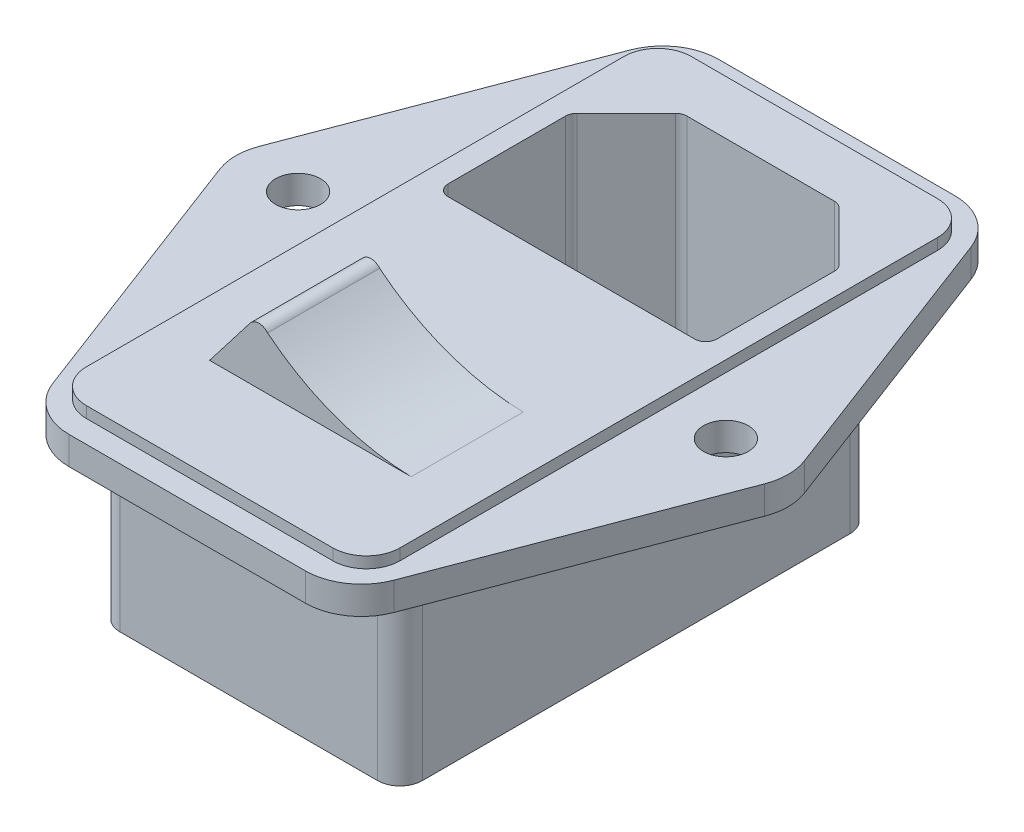
SolidWorks part; units mm, degrees
ref_plane "Front Plane" through (0, 0, 0) normal (0, 0, 1) x (1, 0, 0)
ref_plane "Top Plane" through (0, 0, 0) normal (0, 1, 0) x (1, 0, 0)
ref_plane "Right Plane" through (0, 0, 0) normal (1, 0, 0) x (0, 0, -1)
sketch "Sketch1" plane through (0, 0, 0) normal (0, 1, 0) x (1, 0, 0)
  line L0 (0, 44.6457) -> (0, -41.2867) construction
  line L1 (-19.1, 0) -> (19.1, 0) construction
  line L2 (25, 0) -> (14, -29)
  line L3 (0, 29) -> (14, 29)
  line L4 (14, 29) -> (25, 0)
  line L5 (0, -29) -> (14, -29)
  line L6 (0, 29) -> (0, -29)
  circle A0 centre (19.1, 0) radius 2
  dimension "D1" = 4
  dimension "D2" = 38.2
  dimension "D3" = 58
  dimension "D4" = 14
  dimension "D6" = 50
extrude "Boss-Extrude1" add sketch "Sketch1" against normal blind 2.5
fillet "Fillet1" radius 5 3 edges at (25, -1.25, 0) (14, -1.25, 29) (14, -1.25, -29)
sketch "Sketch2" plane through (0, 0, 0) normal (0, 1, 0) x (1, 0, 0)
  line L0 (0, 29) -> (0, -29) construction
  line L1 (0, 27) -> (11, 27)
  line L2 (0, 27) -> (0, -27)
  line L3 (0, -27) -> (11, -27)
  line L4 (14, 24) -> (14, -24)
  line L5 (0, 0) -> (56.2299, 0) construction
  arc A0 (14, -24) -> (11, -27) centre (11, -24) cw
  arc A1 (11, 27) -> (14, 24) centre (11, 24) cw
  point P13 (14, 27)
  dimension "D3" = 3
  dimension "D1" = 54
  dimension "D2" = 14
extrude "Boss-Extrude2" add sketch "Sketch2" along normal blind 1
sketch "Sketch3" plane through (0, -2.5, 0) normal (0, -1, 0) x (1, 0, 0)
  line L0 (0, -29) -> (0, 29) construction
  line L1 (0, 23.5) -> (13.5, 23.5)
  line L2 (0, 23.5) -> (0, -23.5)
  line L3 (0, -23.5) -> (7.5, -23.5)
  line L4 (13.5, 23.5) -> (13.5, -17.5)
  line L5 (0, 0) -> (10.1538, 0) construction
  line L6 (13.5, -17.5) -> (7.5, -23.5)
  dimension "D1" = 47
  dimension "D2" = 13.5
  dimension "D3" = 7.5
  dimension "D4" = 6
extrude "Boss-Extrude3" add sketch "Sketch3" along normal blind 16
fillet "Fillet2" radius 2 3 edges at (13.5, -10.5, -17.5) (7.5, -10.5, -23.5) (13.5, -10.5, 23.5)
sketch "Sketch5" plane through (0, 1, 0) normal (0, 1, 0) x (1, 0, 0)
  line L0 (0, 27) -> (0, -27) construction
  line L1 (0, 22.2) -> (7, 22.2)
  line L2 (0, 22.2) -> (0, 5.3)
  line L3 (0, 5.3) -> (12, 5.3)
  line L4 (12, 17.2) -> (12, 5.3)
  line L5 (7, 22.2) -> (12, 17.2)
  line L6 (11, 27) -> (0, 27) construction
  dimension "D1" = 12
  dimension "D2" = 4.8
  dimension "D3" = 5
  dimension "D4" = 5
  dimension "D5" = 16.9
extrude "Cut-Extrude1" cut sketch "Sketch5" against normal blind 18
fillet "Fillet3" radius 1 3 edges at (7, -8, -22.2) (12, -8, -17.2) (12, -8, -5.3)
mirror "Mirror1" about plane through (0, -2.5, -29) normal (-1, 0, 0) of bodies 104
sketch "Sketch6" plane through (0, 0, 0) normal (0, 0, 1) x (1, 0, 0)
  line L0 (-9, 1) -> (-5.3831, 5.6832)
  line L1 (-11, 1) -> (11, 1) construction
  line L2 (0, 0) -> (0, 6.1663) construction
  line L3 (-10.5489, 0) -> (10.5489, 0) construction
  line L4 (-9, 1) -> (9, 1)
  arc A0 (-3.8173, 5.7046) -> (9, 1) centre (9.4512, 22.0414) ccw
  arc A1 (-3.8173, 5.7046) -> (-5.3831, 5.6832) centre (-4.5917, 5.0719) ccw
  dimension "D1" = 1
  dimension "D2" = 18
extrude "Boss-Extrude4" add sketch "Sketch6" along normal blind 10 from offset 8
